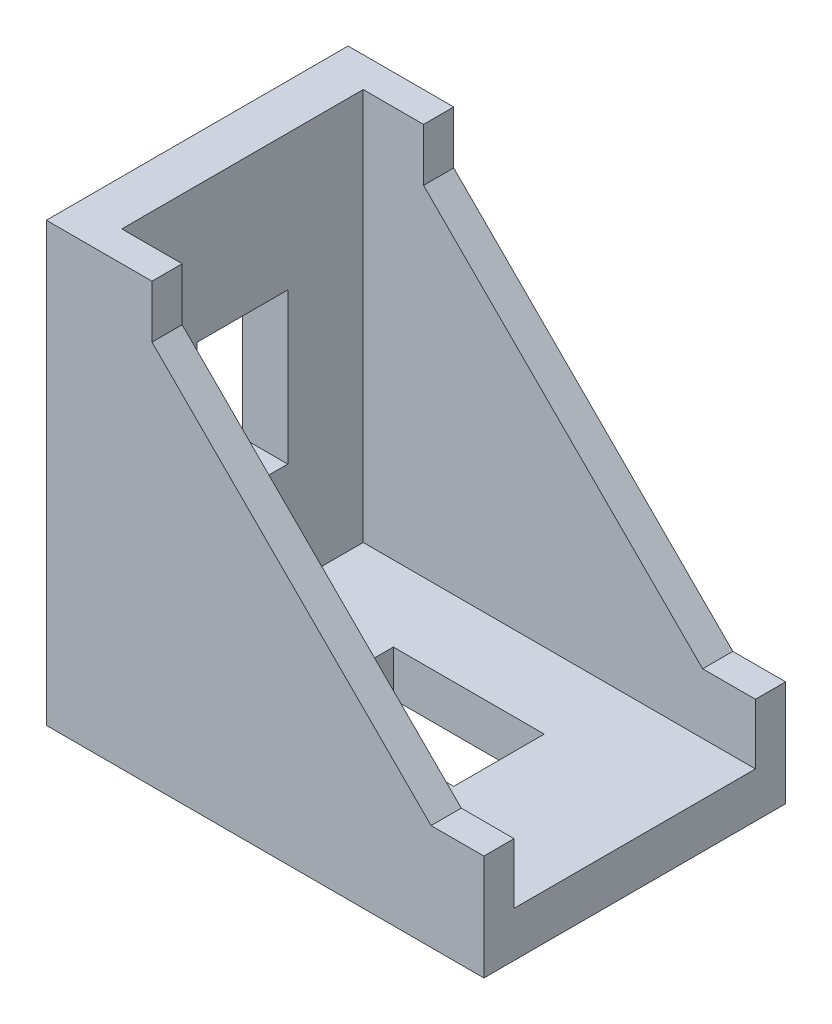
SolidWorks part; units mm, degrees
ref_plane "Front Plane" through (0, 0, 0) normal (0, 0, 1) x (1, 0, 0)
ref_plane "Top Plane" through (0, 0, 0) normal (0, 1, 0) x (1, 0, 0)
ref_plane "Right Plane" through (0, 0, 0) normal (1, 0, 0) x (0, 0, -1)
sketch "Sketch1" plane through (0, 0, 0) normal (0, 0, 1) x (1, 0, 0)
  line L1 (-14.5, -14.5) -> (14.5, -14.5)
  line L2 (-14.5, -14.5) -> (-14.5, 14.5)
  line L3 (-14.5, 14.5) -> (14.5, 14.5)
  line L4 (14.5, -14.5) -> (14.5, 14.5)
  line L5 (-14.5, -14.5) -> (14.5, 14.5) construction
  line L6 (-14.5, 14.5) -> (14.5, -14.5) construction
  point P0 (0, 0)
  dimension "D1" = 29
extrude "Boss-Extrude1" add sketch "Sketch1" along normal blind 20
sketch "Sketch2" plane through (0, 14.5, 0) normal (0, 1, 0) x (1, 0, 0)
  line L0 (14.5, -20) -> (14.5, 0) construction
  line L1 (-11.5, -18) -> (14.5, -18)
  line L2 (-11.5, -18) -> (-11.5, -2)
  line L3 (-11.5, -2) -> (14.5, -2)
  line L4 (14.5, -18) -> (14.5, -2)
  line L5 (-11.5, -18) -> (14.5, -2) construction
  line L6 (-11.5, -2) -> (14.5, -18) construction
  line L7 (-14.5, -20) -> (-14.5, 0) construction
  line L8 (14.5, 0) -> (-14.5, 0) construction
  point P0 (1.5, -10)
  point P7 (0.5, -10)
  point P10 (-14.5, -10)
  point P17 (0, 0)
  dimension "D1" = 3
  dimension "D2" = 2
extrude "Cut-Extrude1" cut sketch "Sketch2" against normal blind 26
sketch "Sketch3" plane through (0, 0, 20) normal (0, 0, 1) x (1, 0, 0)
  line L0 (-7.5, 14.5) -> (-7.5, 11)
  line L1 (14.5, 14.5) -> (-14.5, 14.5) construction
  line L2 (-7.5, 11) -> (11, -7.5)
  line L3 (11, -7.5) -> (14.5, -7.5)
  line L4 (14.5, -14.5) -> (14.5, 14.5) construction
  line L5 (14.5, -7.5) -> (14.5, 14.5)
  line L6 (14.5, 14.5) -> (-7.5, 14.5)
  line L7 (-14.5, 14.5) -> (-14.5, -14.5) construction
  dimension "D1" = 7
  dimension "D2" = 3.5
extrude "Cut-Extrude2" cut sketch "Sketch3" against normal through all
sketch "Sketch4" plane through (0, -14.5, 0) normal (0, -1, 0) x (1, 0, 0)
  line L0 (-14.5, 20) -> (-14.5, 0) construction
  line L1 (-4.5, 13) -> (5.5, 13)
  line L2 (-4.5, 13) -> (-4.5, 7)
  line L3 (-4.5, 7) -> (5.5, 7)
  line L4 (5.5, 13) -> (5.5, 7)
  line L5 (-4.5, 13) -> (5.5, 7) construction
  line L6 (-4.5, 7) -> (5.5, 13) construction
  point P0 (0.5, 10)
  point P5 (0, 0)
  point P8 (-14.5, 10)
  dimension "D1" = 6
  dimension "D2" = 10
  dimension "D3" = 10
extrude "Cut-Extrude3" cut sketch "Sketch4" against normal through all
sketch "Sketch5" plane through (-14.5, 0, 0) normal (-1, 0, 0) x (0, 0, 1)
  line L0 (20, -14.5) -> (0, -14.5) construction
  line L1 (7, 5.5) -> (13, 5.5)
  line L2 (7, 5.5) -> (7, -4.5)
  line L3 (7, -4.5) -> (13, -4.5)
  line L4 (13, 5.5) -> (13, -4.5)
  line L5 (7, 5.5) -> (13, -4.5) construction
  line L6 (7, -4.5) -> (13, 5.5) construction
  point P0 (10, 0.5)
  point P5 (0, 0)
  point P9 (10, -14.5)
  dimension "D1" = 6
  dimension "D2" = 10
  dimension "D3" = 10
extrude "Cut-Extrude4" cut sketch "Sketch5" against normal through all
